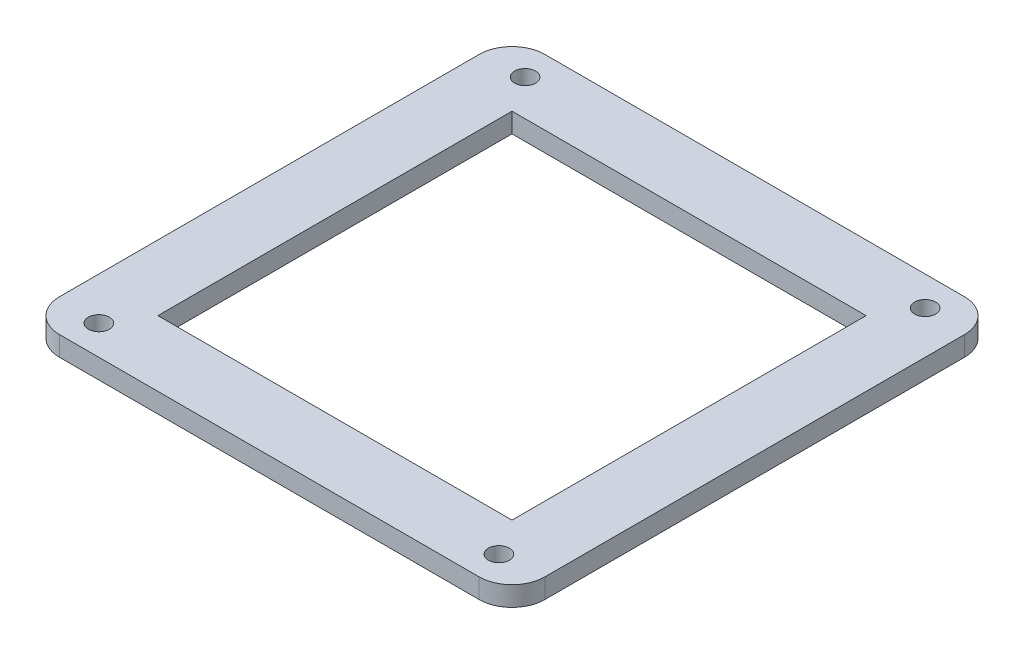
SolidWorks part; units mm, degrees
material "PMMA"
ref_plane "Front Plane" through (0, 0, 0) normal (0, 0, 1) x (1, 0, 0)
ref_plane "Top Plane" through (0, 0, 0) normal (0, 1, 0) x (1, 0, 0)
ref_plane "Right Plane" through (0, 0, 0) normal (1, 0, 0) x (0, 0, -1)
sketch "Sketch1" plane through (0, 0, 0) normal (0, 1, 0) x (1, 0, 0)
  line L0 (-27, 27) -> (27, 27)
  line L1 (-37, -37) -> (37, -37)
  line L2 (-37, -37) -> (-37, 37)
  line L3 (-37, 37) -> (37, 37)
  line L4 (37, -37) -> (37, 37)
  line L5 (-37, -37) -> (37, 37) construction
  line L6 (-37, 37) -> (37, -37) construction
  line L7 (27, -27) -> (27, 27)
  line L8 (-27, -27) -> (27, -27)
  line L9 (-27, -27) -> (-27, 27)
  point P0 (0, 0)
  dimension "D1" = 74
  dimension "D2" = 10
extrude "Boss-Extrude1" add sketch "Sketch1" along normal blind 3
hole_wizard "M3 Clearance Hole1" positions "3DSketch1" profile "Sketch2" hole size "M3" standard "ANSI Metric"
sketch3d "3DSketch1"
  line L2 (37, 3, -37) -> (-37, 3, -37) construction
  line L3 (37, 3, 37) -> (37, 3, -37) construction
  line L4 (-37, 3, 37) -> (37, 3, 37) construction
  point P0 (-30.5, 3, -32.5)
  point P2 (30.5, 3, -32.5)
  point P4 (30.5, 3, 32.5)
  point P6 (-30.5, 3, 32.5)
  dimension "D1" = 4.5
  dimension "D2" = 6.5
  dimension "D3" = 4.5
sketch "Sketch2" plane through (-30.5, 3, -32.5) normal (1, 0, 0) x (0, 0, 1)
  line L0 (0, 0) -> (0, 5.4614)
  line L1 (0, 5.4614) -> (1.6, 4.5)
  line L2 (1.6, 4.5) -> (1.6, 0)
  line L5 (1.6, 0) -> (0, 0)
  line L10 (0, 5.4614) -> (-1.6, 4.5) construction
  line L11 (0, -6.35) -> (0, 107.95) construction
  dimension "Hole Dia." = 3.2
  dimension "Hole Depth" = 4.5
  dimension "Drill Angle" = 118
fillet "Fillet1" radius 5 4 edges at (-37, 1.5, 37) (37, 1.5, 37) (37, 1.5, -37) (-37, 1.5, -37)
